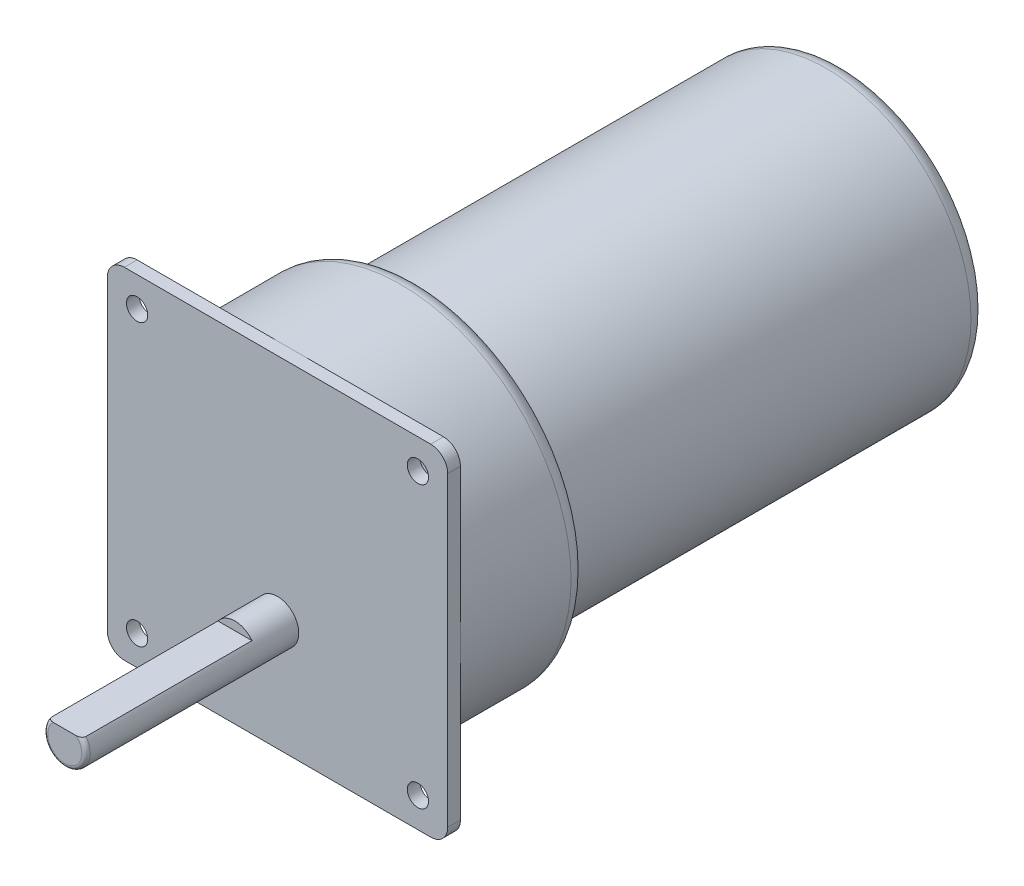
SolidWorks part; units mm, degrees
ref_plane "Front Plane" through (0, 0, 0) normal (0, 0, 1) x (1, 0, 0)
ref_plane "Top Plane" through (0, 0, 0) normal (0, 1, 0) x (1, 0, 0)
ref_plane "Right Plane" through (0, 0, 0) normal (1, 0, 0) x (0, 0, -1)
sketch "Sketch1" plane through (0, 0, 0) normal (0, 0, 1) x (1, 0, 0)
  circle A0 centre (0, 0) radius 40
  dimension "D1" = 80
extrude "Boss-Extrude1" add sketch "Sketch1" along normal blind 30
sketch "Sketch2" plane through (0, 0, 30) normal (0, 0, 1) x (1, 0, 0)
  line L0 (0, 0) -> (13.9236, 0) construction
  line L1 (-40, -40) -> (40, -40)
  line L2 (-40, -40) -> (-40, 40)
  line L3 (-40, 40) -> (40, 40)
  line L4 (40, -40) -> (40, 40)
  line L5 (-40, -40) -> (40, 40) construction
  line L6 (-40, 40) -> (40, -40) construction
  circle A0 centre (0, 0) radius 40 construction
  circle A1 centre (33, -33) radius 2.5
  circle A2 centre (-33, 33) radius 2.5
  circle A3 centre (33, 33) radius 2.5
  circle A4 centre (-33, -33) radius 2.5
  point P0 (0, 0)
  dimension "D1" = 5
  dimension "D2" = 66
extrude "Boss-Extrude2" add sketch "Sketch2" along normal blind 3
fillet "Fillet1" radius 4 4 edges at (-40, 40, 31.5) (40, 40, 31.5) (40, -40, 31.5) (-40, -40, 31.5)
sketch "Sketch3" plane through (0, 0, 0) normal (0, 0, -1) x (-1, 0, 0)
  circle A0 centre (0, 0) radius 34
  dimension "D1" = 68
extrude "Boss-Extrude3" add sketch "Sketch3" along normal blind 100
fillet "Fillet2" radius 4 2 edges at (40, 0, 0) (-34, 0, -100)
sketch "Sketch4" plane through (0, 0, 33) normal (0, 0, 1) x (1, 0, 0)
  line L1 (-36, -40) -> (36, -40) construction
  line L2 (0, -14) -> (0, -33) construction
  line L3 (0, -33) -> (-33, -33) construction
  line L4 (0, -33) -> (33, -33) construction
  circle A0 centre (0, -14) radius 5
  point P4 (0, -14)
  point P9 (0, -9)
  dimension "D1" = 26
  dimension "D2" = 10
extrude "Boss-Extrude4" add sketch "Sketch4" along normal blind 50
fillet "Fillet3" radius 1 1 edges at (5, -14, 83)
sketch "Sketch5" plane through (-40, 0, 0) normal (-1, 0, 0) x (0, 0, 1)
  line L0 (82, -9) -> (33, -9) construction
  line L1 (85.6894, -9) -> (43, -9)
  line L2 (85.6894, -9) -> (85.6894, -11)
  line L3 (85.6894, -11) -> (43, -11)
  line L4 (43, -9) -> (43, -11)
  line L5 (83, -18) -> (83, -10) construction
  point P5 (85.6894, -9.2159)
  dimension "D1" = 2
  dimension "D2" = 40
extrude "Cut-Extrude1" cut sketch "Sketch5" against normal through all
